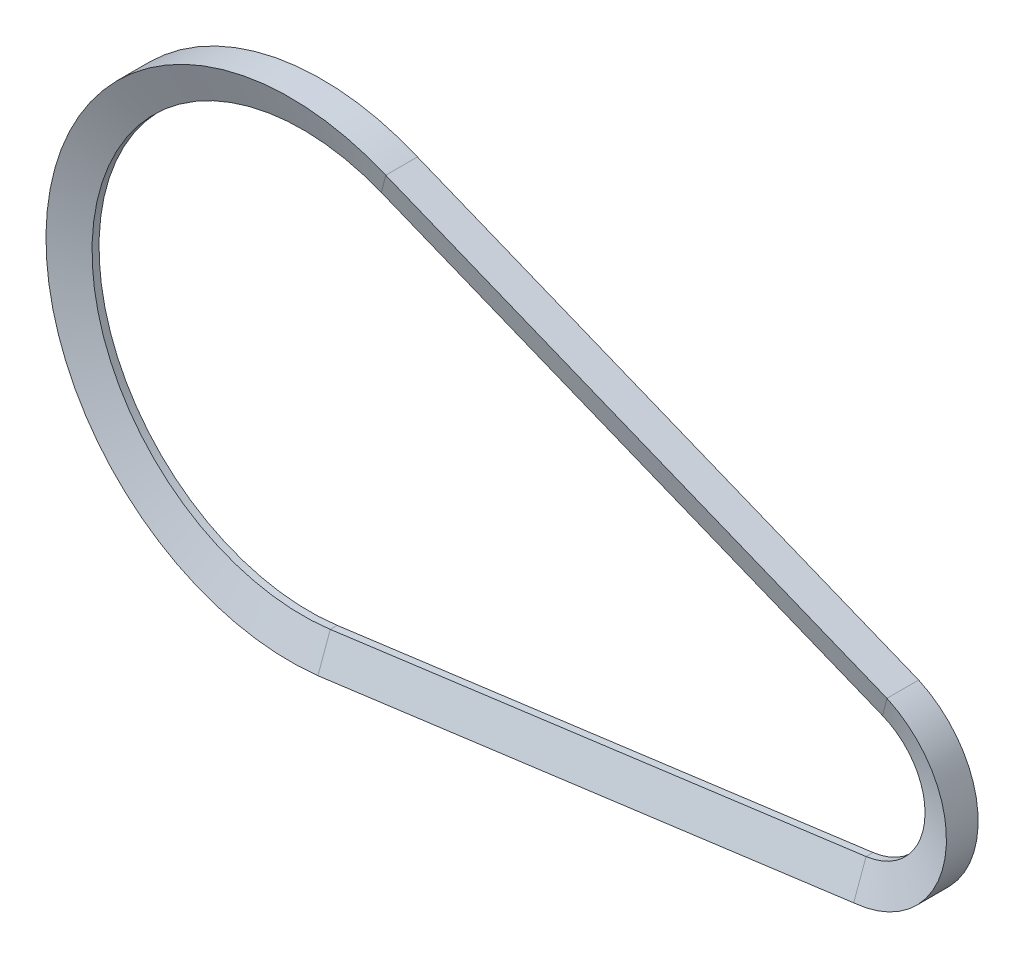
SolidWorks part; units mm, degrees
ref_plane "Front Plane" through (0, 0, 0) normal (0, 0, 1) x (1, 0, 0)
ref_plane "Top Plane" through (0, 0, 0) normal (0, 1, 0) x (1, 0, 0)
ref_plane "Right Plane" through (0, 0, 0) normal (1, 0, 0) x (0, 0, -1)
sketch "Sketch1" plane through (0, 0, 0) normal (0, 0, 1) x (1, 0, 0)
  line L0 (6.1247, -46.0949) -> (124.4757, -30.3693)
  line L1 (17.4127, 43.1167) -> (128.117, -1.5914)
  arc A0 (17.4127, 43.1167) -> (6.1247, -46.0949) centre (0, 0) ccw
  arc A1 (124.4757, -30.3693) -> (128.117, -1.5914) centre (122.5, -15.5) ccw
  dimension "D3" = 93
  dimension "D4" = 30
  dimension "D1" = 15.5
  dimension "D2" = 122.5
ref_plane "Plane1" through (6.1247, 0, 0) normal (1, 0, 0) x (0, 0, -1)
sketch "Sketch2" plane through (6.1247, 0, 0) normal (1, 0, 0) x (0, 0, -1)
  line L0 (0, -46.0949) -> (0, -12.8248) construction
  line L1 (-0.7702, -46.0949) -> (0.7702, -46.0949)
  line L2 (-3.5, -53.5949) -> (3.5, -53.5949)
  line L3 (3.5, -53.5949) -> (0.7702, -46.0949)
  line L4 (-0.7702, -46.0949) -> (-3.5, -53.5949)
  line L5 (0, -46.0949) -> (0, -53.5949) construction
  point P8 (2.0052, -46.0949)
  dimension "D1" = 7
  dimension "D2" = 7.5
  dimension "D3" = 40
sweep "Sweep1" add profiles "Sketch2" path "Sketch1"
